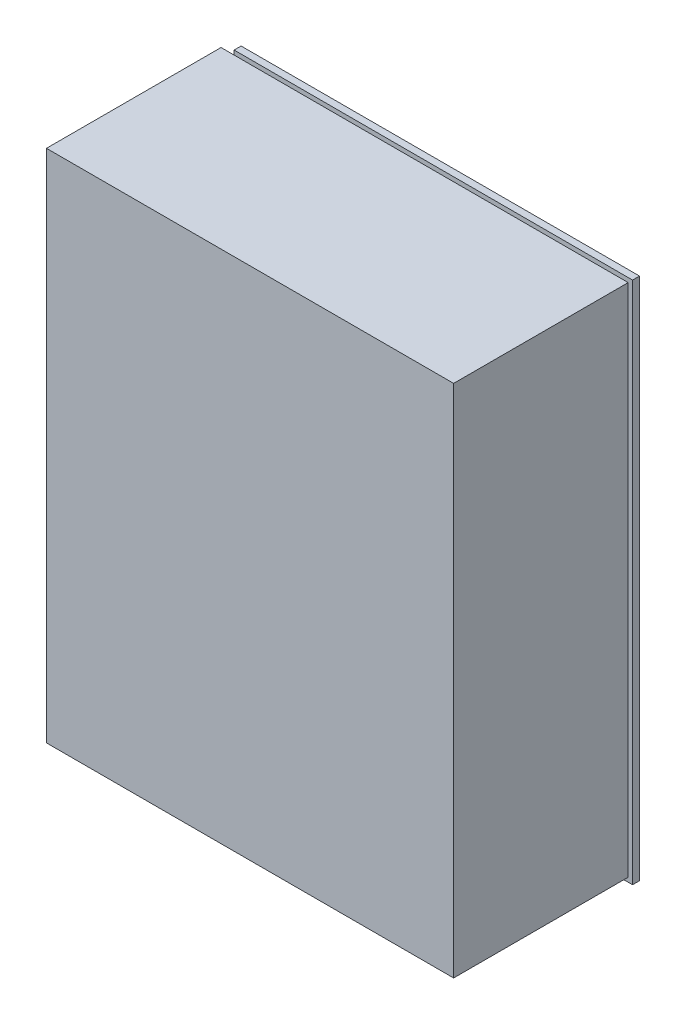
SolidWorks part; units mm, degrees
material "6061 합금"
ref_plane "정면" through (0, 0, 0) normal (0, 0, 1) x (1, 0, 0)
ref_plane "윗면" through (0, 0, 0) normal (0, 1, 0) x (1, 0, 0)
ref_plane "우측면" through (0, 0, 0) normal (1, 0, 0) x (0, 0, -1)
sketch "스케치2" plane through (0, 0, 0) normal (0, 0, 1) x (1, 0, 0)
  line L1 (-47.65, -60) -> (47.65, -60)
  line L2 (-47.65, -60) -> (-47.65, 60)
  line L3 (-47.65, 60) -> (47.65, 60)
  line L4 (47.65, -60) -> (47.65, 60)
  line L5 (-47.65, -60) -> (47.65, 60) construction
  line L6 (-47.65, 60) -> (47.65, -60) construction
  point P0 (0, 0)
  dimension "D1" = 120
  dimension "D2" = 95.3
extrude "보스-돌출2" add sketch "스케치2" along normal blind 1.6
sketch "스케치3" plane through (0, 0, 1.6) normal (0, 0, 1) x (1, 0, 0)
  line L0 (47.65, 60) -> (-47.65, 60) construction
  line L1 (-47.65, 60) -> (-43.65, 60)
  line L2 (-47.65, 60) -> (-47.65, 53)
  line L3 (-47.65, 53) -> (-43.65, 53)
  line L4 (-43.65, 60) -> (-43.65, 53)
  line L5 (-47.65, -60) -> (-41.65, -60)
  line L6 (-47.65, -60) -> (-47.65, -56)
  line L7 (-47.65, -56) -> (-41.65, -56)
  line L8 (-41.65, -60) -> (-41.65, -56)
  line L9 (47.65, -60) -> (47.65, 60) construction
  circle A0 centre (-38.35, 52) radius 1.8
  circle A1 centre (41.65, 52) radius 1.8
  circle A2 centre (41.65, -56) radius 1.8
  circle A3 centre (-43.35, -53) radius 1.8
  point P18 (0, 0)
  point P19 (0, 0)
  point P20 (0, 0)
  point P21 (0, 0)
  point P22 (0, 0)
  point P23 (26.1623, 48.4868)
  point P28 (0, 0)
  dimension "D7" = 3.6
  dimension "D1" = 108
  dimension "D2" = 105
  dimension "D3" = 80
  dimension "D4" = 85
  dimension "D5" = 8
  dimension "D6" = 6
  dimension "D8" = 4
  dimension "D9" = 7
  dimension "D10" = 4
  dimension "D11" = 6
extrude "컷-돌출1" cut sketch "스케치3" against normal through all
sketch "스케치4" plane through (0, 0, 1.6) normal (0, 0, 1) x (1, 0, 0)
  line L8 (-46.65, -59) -> (46.65, -59)
  line L9 (46.65, -59) -> (46.65, 59)
  line L10 (46.65, 59) -> (-46.65, 59)
  line L11 (-46.65, 59) -> (-46.65, -59)
  line L12 (-46.65, -59) -> (46.65, -59)
  line L13 (46.65, -59) -> (46.65, 59)
  line L14 (46.65, 59) -> (-46.65, 59)
  line L15 (-46.65, 59) -> (-46.65, -59)
  dimension "D1" = 1
surface "곡면-돌출1" sketch "스케치4" parameters "D1"=40
surface "곡면 채우기1"
surface "곡면 채우기2"
equation "\"Mass\"= \"SW-질량\" / 1000"
